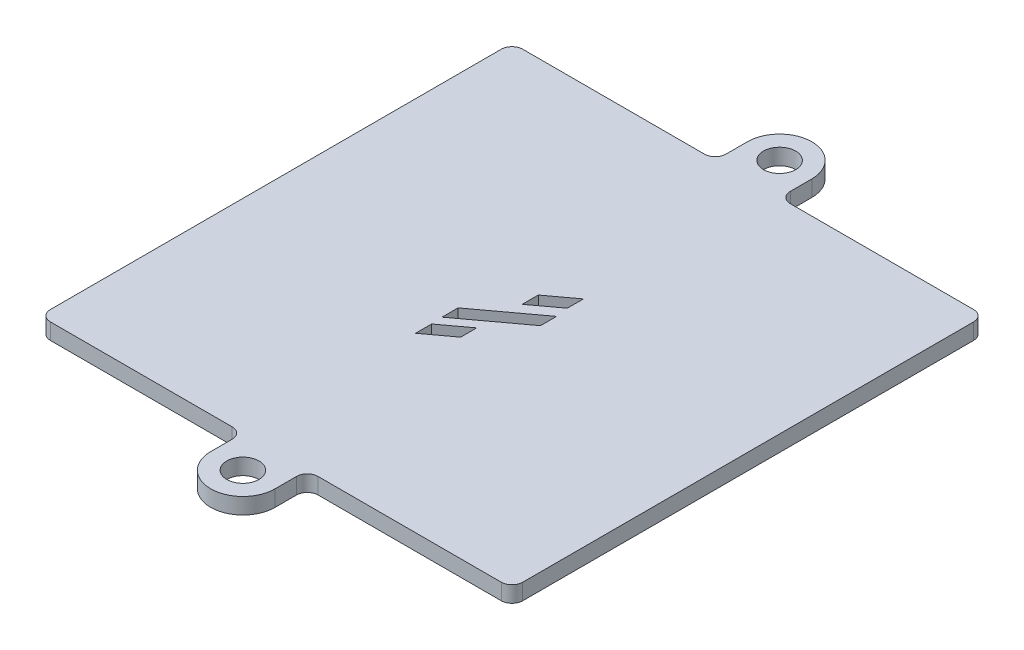
SolidWorks part; units mm, degrees
ref_plane "前视基准面" through (0, 0, 0) normal (0, 0, 1) x (1, 0, 0)
ref_plane "上视基准面" through (0, 0, 0) normal (0, 1, 0) x (1, 0, 0)
ref_plane "右视基准面" through (0, 0, 0) normal (1, 0, 0) x (0, 0, -1)
sketch "草图1" plane through (0, 0, 0) normal (0, 1, 0) x (1, 0, 0)
  line L0 (-22, 44) -> (-22, 0) construction
  line L1 (-1, 0) -> (-18.0696, 0)
  line L2 (0, 1) -> (0, 43)
  line L3 (-1, 44) -> (-18.0696, 44)
  line L4 (-44, 1) -> (-44, 43)
  line L5 (-42.5, 22) -> (-1.5, 22) construction
  line L6 (-1.5, 1.5) -> (-42.5, 1.5) construction
  line L7 (-1.5, 1.5) -> (-1.5, 42.5) construction
  line L8 (-1.5, 42.5) -> (-42.5, 42.5) construction
  line L9 (-42.5, 1.5) -> (-42.5, 42.5) construction
  line L10 (-1.5, 1.5) -> (-42.5, 42.5) construction
  line L11 (-1.5, 42.5) -> (-42.5, 1.5) construction
  line L12 (-25.0696, -3) -> (-25.0696, -1)
  line L13 (-19.0696, -3) -> (-19.0696, -1)
  line L14 (-26.0696, 0) -> (-43, 0)
  line L15 (-25.0696, 47) -> (-25.0696, 45)
  line L16 (-19.0696, 47) -> (-19.0696, 45)
  line L17 (-26.0696, 44) -> (-43, 44)
  line L18 (-22, 44) -> (-22.0696, 44)
  line L19 (-19.8699, 24.0219) -> (-19.8699, 22.5205)
  line L20 (-19.8699, 24.0219) -> (-25.1441, 20.1218)
  line L21 (-19.8699, 22.5205) -> (-25.1441, 18.6205)
  line L22 (-25.1441, 20.1218) -> (-25.1441, 18.6205)
  line L23 (-20.0266, 26.6825) -> (-20.0266, 25.1812)
  line L24 (-20.0266, 26.6825) -> (-22.444, 24.8949)
  line L25 (-20.0266, 25.1812) -> (-22.444, 23.3936)
  line L26 (-22.444, 24.8949) -> (-22.444, 23.3936)
  line L27 (-22.6594, 19.3774) -> (-22.6594, 17.8761)
  line L28 (-22.6594, 19.3774) -> (-25.0768, 17.5898)
  line L29 (-22.6594, 17.8761) -> (-25.0768, 16.0885)
  line L30 (-25.0768, 17.5898) -> (-25.0768, 16.0885)
  arc A0 (-1, 0) -> (0, 1) centre (-1, 1) ccw
  arc A1 (0, 43) -> (-1, 44) centre (-1, 43) ccw
  arc A2 (-43, 44) -> (-44, 43) centre (-43, 43) ccw
  arc A3 (-43, 0) -> (-44, 1) centre (-43, 1) cw
  circle A4 centre (-22.0696, -3) radius 1.5
  circle A5 centre (-22.0696, 47) radius 1.5
  arc A6 (-25.0696, -3) -> (-19.0696, -3) centre (-22.0696, -3) ccw
  arc A7 (-19.0696, 47) -> (-25.0696, 47) centre (-22.0696, 47) ccw
  arc A8 (-19.0696, -1) -> (-18.0696, 0) centre (-18.0696, -1) cw
  arc A9 (-25.0696, -1) -> (-26.0696, 0) centre (-26.0696, -1) ccw
  arc A10 (-19.0696, 45) -> (-18.0696, 44) centre (-18.0696, 45) ccw
  arc A11 (-25.0696, 45) -> (-26.0696, 44) centre (-26.0696, 45) cw
  point P7 (0, 0)
  point P10 (0, 44)
  point P15 (-44, 0)
  point P18 (-22, 22)
  point P40 (-19.0696, 0)
  point P43 (-25.0696, 0)
  point P48 (-25.0696, 44)
  dimension "D3" = 1
  dimension "D6" = 4.5
  dimension "D7" = 1
  dimension "D1" = 44
  dimension "D2" = 44
  dimension "D4" = 41
  dimension "D5" = 41
extrude "凸台-拉伸1" add sketch "草图1" along normal blind 1.5
